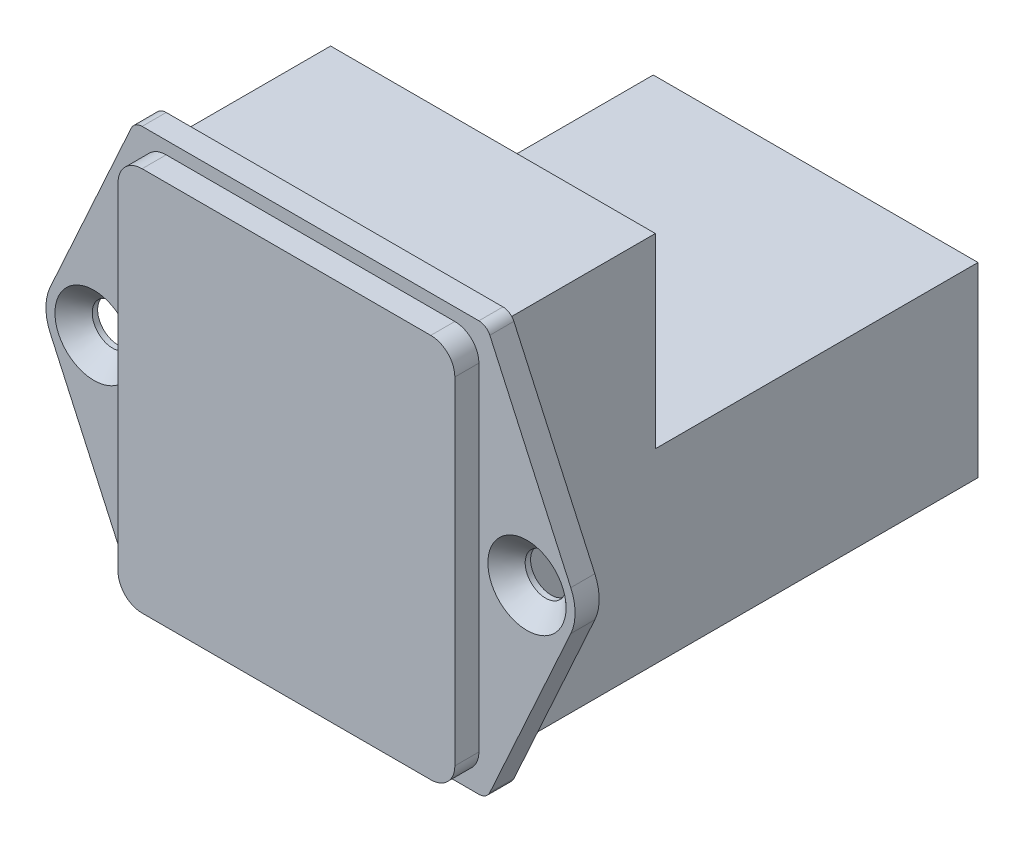
SolidWorks part; units mm, degrees
ref_plane "Front Plane" through (0, 0, 0) normal (0, 0, 1) x (1, 0, 0)
ref_plane "Top Plane" through (0, 0, 0) normal (0, 1, 0) x (1, 0, 0)
ref_plane "Right Plane" through (0, 0, 0) normal (1, 0, 0) x (0, 0, -1)
sketch "Sketch1" plane through (0, 0, 0) normal (0, 0, 1) x (1, 0, 0)
  line L0 (-21.6415, 1.6552) -> (-14.9104, 16.4638)
  line L1 (-14, 17.05) -> (14, 17.05)
  line L2 (14.9104, 16.4638) -> (21.6415, 1.6552)
  line L3 (21.6415, -1.6552) -> (14.9104, -16.4638)
  line L4 (14, -17.05) -> (-14, -17.05)
  line L5 (-14.9104, -16.4638) -> (-21.6415, -1.6552)
  line L6 (0, 17.05) -> (0, 0) construction
  line L7 (0, 0) -> (0, -17.05) construction
  line L8 (-18, 0) -> (0, 0) construction
  line L9 (0, 0) -> (18, 0) construction
  circle A0 centre (-18, 0) radius 1.5
  circle A1 centre (18, 0) radius 1.5
  arc A2 (-21.6415, 1.6552) -> (-21.6415, -1.6552) centre (-18, 0) ccw
  arc A3 (21.6415, -1.6552) -> (21.6415, 1.6552) centre (18, 0) ccw
  arc A4 (-14, -17.05) -> (-14.9104, -16.4638) centre (-14, -16.05) cw
  arc A5 (14.9104, -16.4638) -> (14, -17.05) centre (14, -16.05) cw
  arc A6 (14, 17.05) -> (14.9104, 16.4638) centre (14, 16.05) cw
  arc A7 (-14.9104, 16.4638) -> (-14, 17.05) centre (-14, 16.05) cw
  point P22 (16.8472, 17.05)
  point P25 (-14.6439, 17.05)
  dimension "D3" = 4
  dimension "D5" = 3
  dimension "D6" = 1
  dimension "D1" = 34.1
  dimension "D2" = 36
  dimension "D4" = 28
extrude "Boss-Extrude1" add sketch "Sketch1" along normal blind 2
sketch "Sketch2" plane through (0, 0, 2) normal (0, 0, 1) x (1, 0, 0)
  line L0 (-12, 14) -> (12, -14) construction
  line L1 (-12, 16) -> (12, 16)
  line L2 (-14, 14) -> (-14, -14)
  line L3 (-12, -16) -> (12, -16)
  line L4 (14, 14) -> (14, -14)
  arc A0 (-14, -14) -> (-12, -16) centre (-12, -14) ccw
  arc A1 (12, -16) -> (14, -14) centre (12, -14) ccw
  arc A2 (12, 16) -> (14, 14) centre (12, 14) cw
  arc A3 (-12, 16) -> (-14, 14) centre (-12, 14) ccw
  dimension "D1" = 2
  dimension "D2" = 28
  dimension "D3" = 32
extrude "Boss-Extrude2" add sketch "Sketch2" along normal blind 2
sketch "Sketch3" plane through (0, 0, 0) normal (1, 0, 0) x (0, 0, -1)
  line L0 (0, 15.5) -> (13.1716, 15.5)
  line L1 (0, 1.6552) -> (0, 16.4638) construction
  line L2 (13.1716, 15.5) -> (13.1716, 0)
  line L3 (13.1716, 0) -> (40, 0)
  line L4 (40, 0) -> (40, -15.5)
  line L5 (40, -15.5) -> (0, -15.5)
  line L6 (0, -16.4638) -> (0, -1.6552) construction
  line L7 (0, -15.5) -> (0, 15.5)
  dimension "D1" = 40
  dimension "D2" = 13.1716
  dimension "D3" = 31
extrude "Boss-Extrude3" add sketch "Sketch3" along normal mid plane 27
hole_wizard "CSK for M3 Flat Head Machine Screw1" positions "Sketch5" profile "Sketch4" countersink size "M3" standard "Ansi Metric" end condition through all
sketch "Sketch5" plane through (0, 0, 2) normal (0, 0, 1) x (1, 0, 0)
  point P0 (-18, 0)
  point P1 (18, 0)
sketch "Sketch4" plane through (-18, 0, 2) normal (1, 0, 0) x (0, -1, 0)
  line L0 (0, 0) -> (0, 42)
  line L1 (0, 42) -> (1.7, 42)
  line L2 (1.7, 42) -> (1.7, 1.55)
  line L3 (1.7, 1.55) -> (3.25, 0)
  line L5 (3.25, 0) -> (0, 0)
  line L6 (-1.7, 1.55) -> (-3.25, 0) construction
  line L11 (0, -6.35) -> (0, 107.95) construction
  dimension "Thru Hole Dia." = 3.4
  dimension "Thru Hole Depth" = 42
  dimension "Near C'Sink Dia." = 6.5
  dimension "Near C'Sink Angle" = 90
